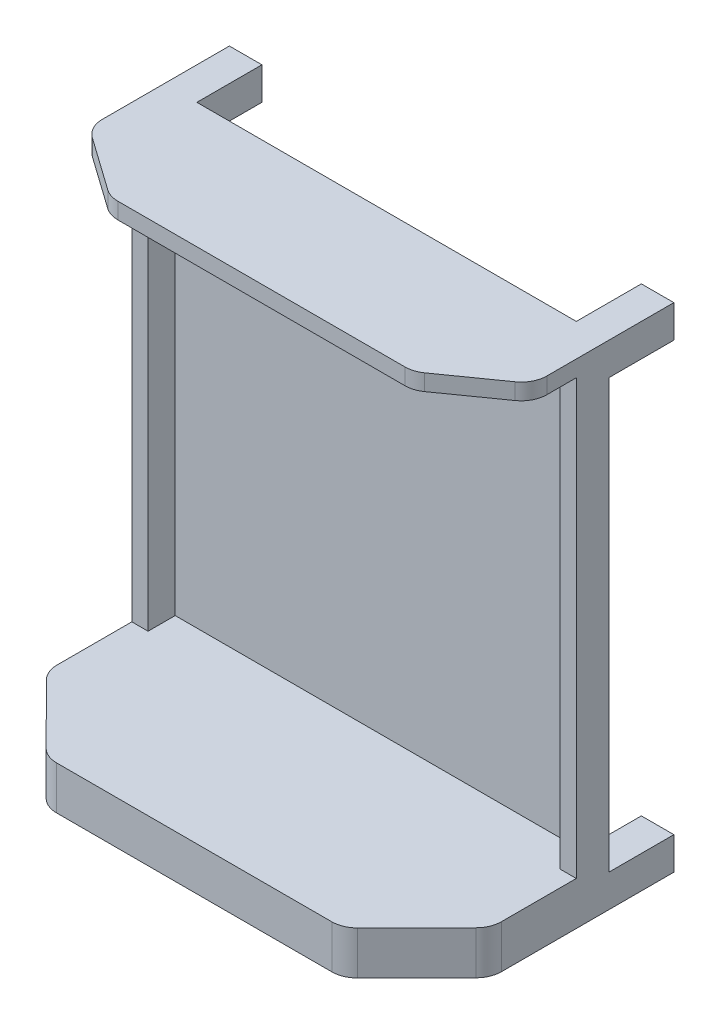
SolidWorks part; units mm, degrees
ref_plane "Front Plane" through (0, 0, 0) normal (0, 0, 1) x (1, 0, 0)
ref_plane "Top Plane" through (0, 0, 0) normal (0, 1, 0) x (1, 0, 0)
ref_plane "Right Plane" through (0, 0, 0) normal (1, 0, 0) x (0, 0, -1)
sketch "Sketch1" plane through (0, 0, 0) normal (0, 0, 1) x (1, 0, 0)
  line L0 (-76.2, -76.2) -> (-76.2, 2108.2)
  line L1 (0, 0) -> (1930.4, 0)
  line L2 (0, 0) -> (0, 2032)
  line L3 (0, 2032) -> (1930.4, 2032)
  line L4 (1930.4, 0) -> (1930.4, 2032)
  line L5 (-76.2, 2108.2) -> (2006.6, 2108.2)
  line L6 (2006.6, -76.2) -> (2006.6, 2108.2)
  line L7 (-76.2, -76.2) -> (2006.6, -76.2)
  line L9 (2006.6, -76.2) -> (-76.2, -76.2)
  line L10 (2006.6, -76.2) -> (2006.6, -203.2)
  line L11 (2006.6, -203.2) -> (-76.2, -203.2)
  line L12 (-76.2, -76.2) -> (-76.2, -203.2)
  dimension "D1" = 2032
  dimension "D2" = 1930.4
  dimension "D4" = 127
  dimension "D3" = 76.2
extrude "Boss-Extrude1" add sketch "Sketch1" along normal blind 127 contours L7 L12 L11 L10 | L0 L7 L6 L5 L4 L1 L2 L3
sketch "Sketch2" plane through (0, 0, 0) normal (0, 0, -1) x (-1, 0, 0)
  line L1 (76.2, 2108.2) -> (-2006.6, 2108.2)
  line L2 (76.2, 2108.2) -> (76.2, -76.2)
  line L4 (-2006.6, 2108.2) -> (-2006.6, -76.2)
  line L5 (76.2, -203.2) -> (-2006.6, -203.2)
  line L6 (76.2, -203.2) -> (76.2, -76.2)
  line L8 (-2006.6, -203.2) -> (-2006.6, -76.2)
  point P5 (0, 0)
  point P8 (0, 0)
  point P10 (0, 0)
  point P11 (0, 0)
  point P13 (0, 0)
extrude "Boss-Extrude2" add sketch "Sketch2" along normal blind 25.4
sketch "Sketch3" plane through (0, 0, 127) normal (0, 0, 1) x (1, 0, 0)
  line L5 (-76.2, 2108.2) -> (-76.2, -203.2) construction
  line L6 (2006.6, -203.2) -> (-76.2, -203.2)
  line L7 (2006.6, -203.2) -> (2006.6, 0)
  line L8 (2006.6, 0) -> (-76.2, 0)
  line L9 (-76.2, -203.2) -> (-76.2, 0)
extrude "Boss-Extrude3" add sketch "Sketch3" along normal blind 400
sketch "Sketch4" plane through (0, 0, 127) normal (0, 0, 1) x (1, 0, 0)
  line L0 (2006.6, 2108.2) -> (2006.6, 0) construction
  line L1 (-76.2, 2108.2) -> (2006.6, 2108.2)
  line L2 (-76.2, 2108.2) -> (-76.2, 2032)
  line L3 (-76.2, 2032) -> (2006.6, 2032)
  line L4 (2006.6, 2108.2) -> (2006.6, 2032)
extrude "Boss-Extrude4" add sketch "Sketch4" along normal blind 200
sketch "Sketch5" plane through (0, 0, 0) normal (0, 1, 0) x (1, 0, 0)
  line L0 (965.2, -527) -> (965.2, -1241.209) construction
  line L1 (2006.6, -527) -> (-76.2, -527) construction
  line L2 (2006.6, -527) -> (1659.61, -875.6356)
  line L3 (1659.61, -875.6356) -> (270.79, -875.6356)
  line L4 (-76.2, -527) -> (270.79, -875.6356)
  line L5 (2006.6, -527) -> (-76.2, -527)
  point P8 (1659.61, -875.6356)
  point P10 (965.2, -875.6356)
extrude "Boss-Extrude5" add sketch "Sketch5" against normal up to surface (203.2 mm away) up to face at (965.2, -203.2, 250.8)
sketch "Sketch6" plane through (0, 2108.2, 0) normal (0, 1, 0) x (1, 0, 0)
  line L0 (965.2, -327) -> (965.2, -843.758)
  line L1 (2006.6, -327) -> (-76.2, -327) construction
  line L2 (2006.6, -327) -> (1676.2113, -560.8099)
  line L3 (1676.2113, -560.8099) -> (254.1887, -560.8099)
  line L4 (-76.2, -327) -> (254.1887, -560.8099)
  line L5 (2006.6, -327) -> (-76.2, -327)
  point P8 (1621.0638, -599.8368)
  point P10 (965.2, -560.8099)
  line M7 (-76.2, -327) -> (2006.6, -327)
extrude "Boss-Extrude6" add sketch "Sketch6" against normal up to surface (76.2 mm away) contours L4 L3 L0 M7 | L3 L2 L0 M7 up to face at (965.2, 2032, 145.25)
fillet "Fillet1" radius 120 8 edges at (254.1887, 2070.1, 560.8099) (-76.2, 2070.1, 327) (1676.2113, 2070.1, 560.8099) (2006.6, 2070.1, 327) (-76.2, -101.6, 527) (270.79, -101.6, 875.6356) (2006.6, -101.6, 527) (1659.61, -101.6, 875.6356)
sketch "Sketch7" plane through (0, 0, -25.4) normal (0, 0, -1) x (-1, 0, 0)
  line L0 (-965.2, 2108.2) -> (-965.2, 1703.5121) construction
  line L1 (76.2, 2108.2) -> (-76.2, 2108.2)
  line L2 (76.2, 2108.2) -> (76.2, 1955.8)
  line L3 (76.2, 1955.8) -> (-76.2, 1955.8)
  line L4 (-76.2, 2108.2) -> (-76.2, 1955.8)
  line L5 (76.2, 2108.2) -> (-2006.6, 2108.2) construction
  line L6 (-2006.6, 952.5) -> (-1457.9183, 952.5) construction
  line L7 (-2006.6, 2108.2) -> (-2006.6, -203.2) construction
  line L8 (-1854.2, 2108.2) -> (-1854.2, 1955.8)
  line L9 (-2006.6, 1955.8) -> (-1854.2, 1955.8)
  line L10 (-2006.6, 2108.2) -> (-2006.6, 1955.8)
  line L11 (-2006.6, 2108.2) -> (-1854.2, 2108.2)
  line L12 (-76.2, -203.2) -> (-76.2, -50.8)
  line L13 (76.2, -50.8) -> (-76.2, -50.8)
  line L14 (76.2, -203.2) -> (76.2, -50.8)
  line L15 (76.2, -203.2) -> (-76.2, -203.2)
  line L16 (-2006.6, -203.2) -> (-1854.2, -203.2)
  line L17 (-2006.6, -203.2) -> (-2006.6, -50.8)
  line L18 (-2006.6, -50.8) -> (-1854.2, -50.8)
  line L19 (-1854.2, -203.2) -> (-1854.2, -50.8)
  dimension "D1" = 152.4
extrude "Boss-Extrude7" add sketch "Sketch7" along normal blind 304.8
